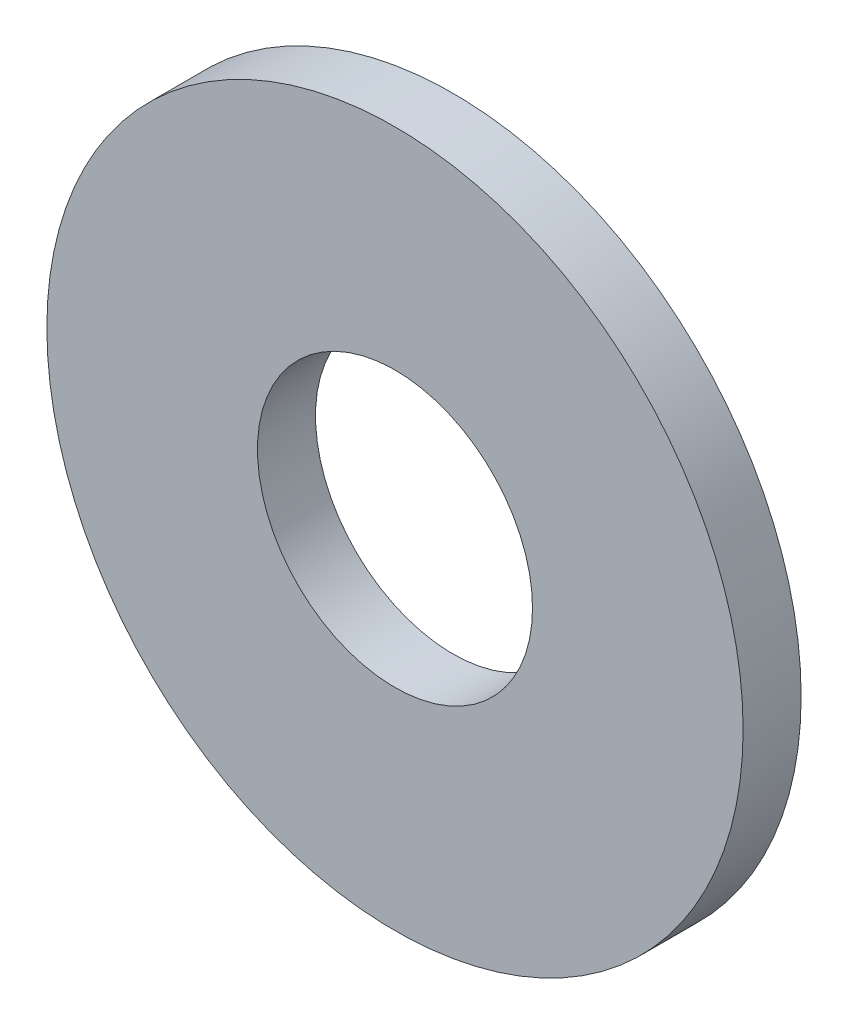
SolidWorks part; units mm, degrees
ref_plane "Front Plane" through (0, 0, 0) normal (0, 0, 1) x (1, 0, 0)
ref_plane "Top Plane" through (0, 0, 0) normal (0, 1, 0) x (1, 0, 0)
ref_plane "Right Plane" through (0, 0, 0) normal (1, 0, 0) x (0, 0, -1)
sketch "Sketch2" plane through (0, 0, 0) normal (0, 0, 1) x (1, 0, 0)
  circle A0 centre (0, 0) radius 38.1
  dimension "D1" = 76.2
extrude "Boss-Extrude1" add sketch "Sketch2" along normal blind 6.35
sketch "Sketch3" plane through (0, 0, 6.35) normal (0, 0, 1) x (1, 0, 0)
  circle A0 centre (0, 0) radius 15.05
  dimension "D1" = 30.1
extrude "Cut-Extrude1" cut sketch "Sketch3" against normal blind 6.35
